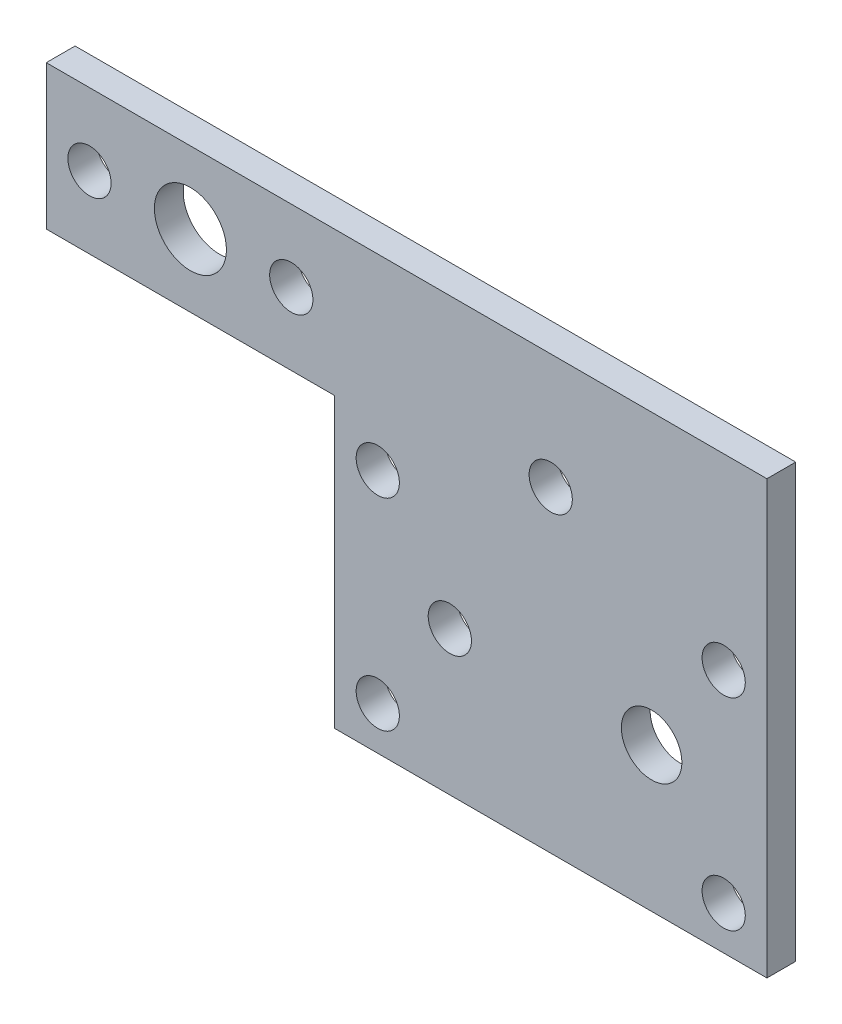
SolidWorks part; units mm, degrees
material "1060 Alloy"
ref_plane "Front Plane" through (0, 0, 0) normal (0, 0, 1) x (1, 0, 0)
ref_plane "Top Plane" through (0, 0, 0) normal (0, 1, 0) x (1, 0, 0)
ref_plane "Right Plane" through (0, 0, 0) normal (1, 0, 0) x (0, 0, -1)
sketch "Sketch1" plane through (0, 0, 0) normal (0, 0, 1) x (1, 0, 0)
  line L1 (20, 0) -> (50, 0)
  line L2 (0, 20) -> (0, 30)
  line L3 (0, 30) -> (50, 30)
  line L4 (50, 0) -> (50, 30)
  line L7 (0, 20) -> (20, 20)
  line L8 (20, 0) -> (20, 20)
  circle A0 centre (23, 17) radius 1.5
  circle A1 centre (23, 3) radius 1.5
  circle A2 centre (47, 3) radius 1.5
  circle A3 centre (47, 17) radius 1.5
  circle A4 centre (3, 25) radius 1.5
  circle A5 centre (17, 25) radius 1.5
  circle A6 centre (28, 10) radius 1.5
  circle A7 centre (35, 22) radius 1.5
  circle A8 centre (42, 10) radius 2.1
  circle A9 centre (10, 25) radius 2.5
  dimension "D1" = 20
  dimension "D3" = 10
  dimension "D4" = 3
  dimension "D13" = 4.2
  dimension "D14" = 3
  dimension "D24" = 10
  dimension "D25" = 5
  dimension "D5" = 5
  dimension "D6" = 3
  dimension "D7" = 3
  dimension "D8" = 3
  dimension "D9" = 30
  dimension "D10" = 17
  dimension "D11" = 3
  dimension "D12" = 17
  dimension "D15" = 15
  dimension "D16" = 8
  dimension "D17" = 8
  dimension "D18" = 10
  dimension "D19" = 8
  dimension "D20" = 10
  dimension "D21" = 20
  dimension "D22" = 20
  dimension "D23" = 20
extrude "Boss-Extrude1" add sketch "Sketch1" along normal blind 2
